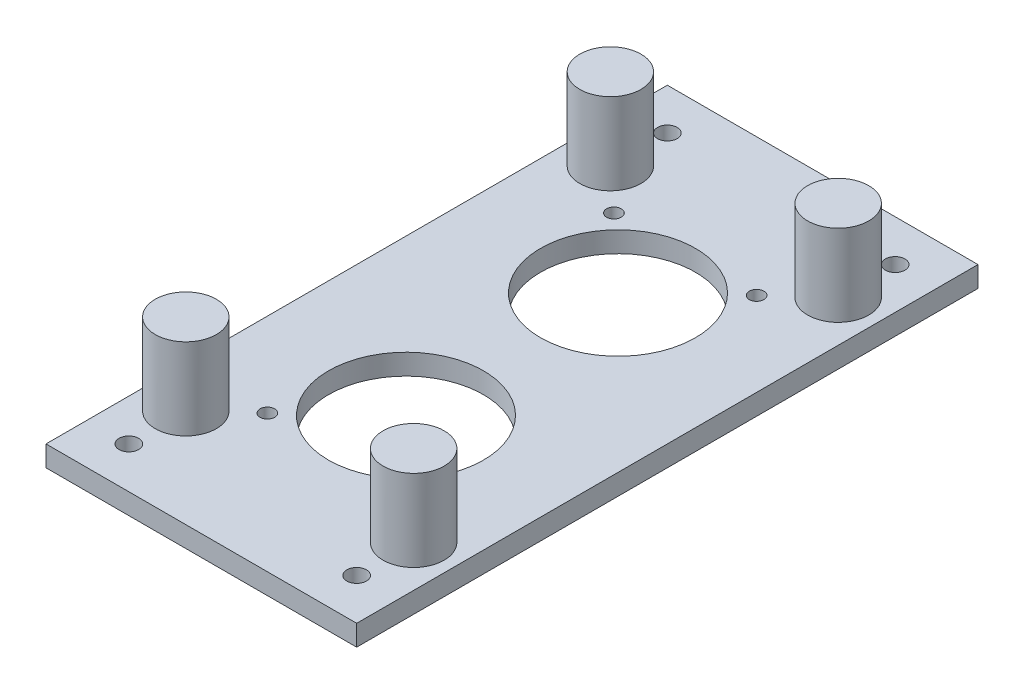
SolidWorks part; units mm, degrees
ref_plane "Front Plane" through (0, 0, 0) normal (0, 0, 1) x (1, 0, 0)
ref_plane "Top Plane" through (0, 0, 0) normal (0, 1, 0) x (1, 0, 0)
ref_plane "Right Plane" through (0, 0, 0) normal (1, 0, 0) x (0, 0, -1)
sketch "Sketch1" plane through (0, 0, 0) normal (0, 1, 0) x (1, 0, 0)
  line L1 (-19.05, -38.1) -> (19.05, -38.1)
  line L2 (-19.05, -38.1) -> (-19.05, 38.1)
  line L3 (-19.05, 38.1) -> (19.05, 38.1)
  line L4 (19.05, -38.1) -> (19.05, 38.1)
  line L5 (-19.05, -38.1) -> (19.05, 38.1) construction
  line L6 (-19.05, 38.1) -> (19.05, -38.1) construction
  point P0 (0, 0)
  dimension "D1" = 76.2
  dimension "D2" = 38.1
extrude "Boss-Extrude1" add sketch "Sketch1" along normal blind 2.54
hole_wizard "Ø1.0mm Dowel Hole1" positions "Sketch2" profile "Sketch3" hole size "Ø1.0" standard "ISO" end condition through all
sketch "Sketch2" plane through (0, 2.54, 0) normal (0, 1, 0) x (1, 0, 0)
  line L0 (0, 13) -> (0, -13) construction
  point P0 (0, -13)
  point P2 (0, 13)
  point P8 (0, 0)
  dimension "D1" = 26
sketch "Sketch3" plane through (0, 2.54, 13) normal (1, 0, 0) x (0, 0, 1)
  line L0 (0, 0) -> (0, 2.54)
  line L1 (0, 2.54) -> (9.5, 2.54)
  line L2 (9.5, 2.54) -> (9.5, 0)
  line L5 (9.5, 0) -> (0, 0)
  line L11 (0, -6.35) -> (0, 107.95) construction
  dimension "Thru Hole Dia." = 19
  dimension "Thru Hole Depth" = 2.54
hole_wizard "M1.6 Clearance Hole1" positions "Sketch5" profile "Sketch6" hole size "M1.6" standard "ANSI Metric" end condition through all
sketch "Sketch5" plane through (0, 2.54, 0) normal (0, 1, 0) x (1, 0, 0)
  line L1 (-8.75, -21.25) -> (8.75, -21.25)
  line L2 (-8.75, -21.25) -> (-8.75, 21.25)
  line L3 (-8.75, 21.25) -> (8.75, 21.25)
  line L4 (8.75, -21.25) -> (8.75, 21.25)
  line L5 (-8.75, -21.25) -> (8.75, 21.25) construction
  line L6 (-8.75, 21.25) -> (8.75, -21.25) construction
  point P0 (8.75, 21.25)
  point P2 (8.75, -21.25)
  point P4 (-8.75, -21.25)
  point P6 (-8.75, 21.25)
  point P52 (0, 0)
  dimension "D1" = 42.5
  dimension "D2" = 17.5
sketch "Sketch6" plane through (8.75, 2.54, -21.25) normal (1, 0, 0) x (0, 0, 1)
  line L0 (0, 0) -> (0, 2.54)
  line L1 (0, 2.54) -> (0.9, 2.54)
  line L2 (0.9, 2.54) -> (0.9, 0)
  line L5 (0.9, 0) -> (0, 0)
  line L11 (0, -6.35) -> (0, 107.95) construction
  dimension "Thru Hole Dia." = 1.8
  dimension "Thru Hole Depth" = 2.54
hole_wizard "M2 Clearance Hole4" positions "Sketch13" profile "Sketch14" hole size "M2" standard "ANSI Metric" end condition through all
sketch "Sketch13" plane through (0, 2.54, 0) normal (0, 1, 0) x (1, 0, 0)
  line L12 (-16.51, -35.56) -> (16.51, -35.56)
  line L13 (16.51, -35.56) -> (16.51, 35.56)
  line L14 (16.51, 35.56) -> (-16.51, 35.56)
  line L15 (-16.51, 35.56) -> (-16.51, -35.56)
  line L16 (-16.51, -35.56) -> (16.51, -35.56) construction
  line L17 (16.51, -35.56) -> (16.51, 35.56) construction
  line L18 (16.51, 35.56) -> (-16.51, 35.56) construction
  line L19 (-16.51, 35.56) -> (-16.51, -35.56) construction
  line L20 (-13.97, 33.02) -> (-13.97, -33.02) construction
  line L21 (-13.97, -33.02) -> (13.97, -33.02) construction
  line L22 (13.97, -33.02) -> (13.97, 33.02) construction
  line L23 (13.97, 33.02) -> (-13.97, 33.02) construction
  point P0 (-13.97, 33.02)
  point P2 (13.97, 33.02)
  point P34 (-13.97, -33.02)
  point P36 (13.97, -33.02)
  dimension "D1" = 2.54
  dimension "D2" = 2.54
sketch "Sketch14" plane through (-13.97, 2.54, -33.02) normal (1, 0, 0) x (0, 0, 1)
  line L0 (0, 0) -> (0, 2.54)
  line L1 (0, 2.54) -> (1.2, 2.54)
  line L2 (1.2, 2.54) -> (1.2, 0)
  line L5 (1.2, 0) -> (0, 0)
  line L11 (0, -6.35) -> (0, 107.95) construction
  dimension "Thru Hole Dia." = 2.4
  dimension "Thru Hole Depth" = 2.54
sketch "Sketch15" plane through (0, 2.54, 0) normal (0, 1, 0) x (1, 0, 0)
  line L0 (-13.97, -26.035) -> (13.97, -26.035) construction
  line L1 (-19.05, -38.1) -> (19.05, -38.1) construction
  line L2 (-13.97, -26.035) -> (-13.97, -33.02) construction
  circle A0 centre (-13.97, -26.035) radius 3.75
  circle A1 centre (13.97, -26.035) radius 3.75
  point P7 (0, -38.1)
  point P8 (0, -26.035)
  point P9 (13.8419, -27.3322)
  dimension "D1" = 7.5
  dimension "D2" = 6.985
extrude "Boss-Extrude2" add sketch "Sketch15" along normal blind 10
mirror "Mirror1" about plane through (0, 0, 0) normal (0, 0, 1) of "Boss-Extrude2"
equation "\"D2@Sketch5\"=17.5mm"
equation "\"D1@Sketch5\"=42.5mm"
equation "\"D1@Sketch2\"=26mm"
equation "\"D1@Sketch15\"=7.5mm"
equation "\"D1@Boss-Extrude2\"=10mm"
